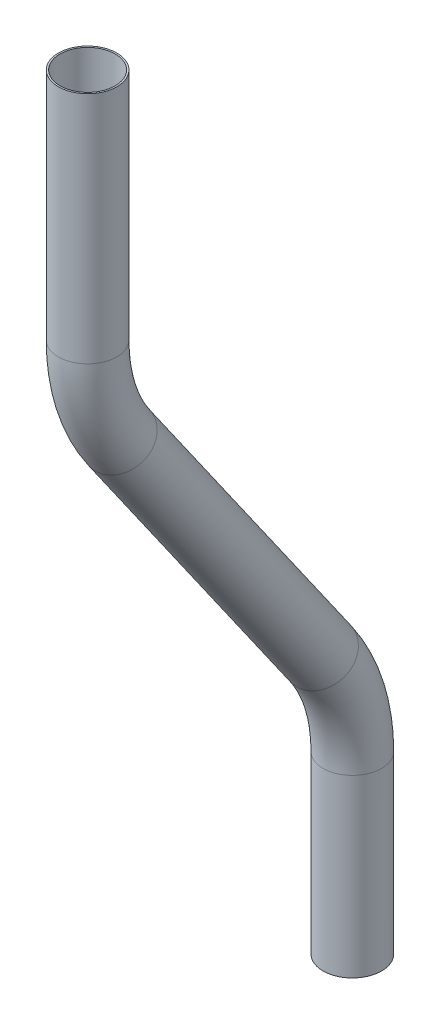
SolidWorks part; units mm, degrees
ref_plane "Front Plane" through (0, 0, 0) normal (0, 0, 1) x (1, 0, 0)
ref_plane "Top Plane" through (0, 0, 0) normal (0, 1, 0) x (1, 0, 0)
ref_plane "Right Plane" through (0, 0, 0) normal (1, 0, 0) x (0, 0, -1)
sketch "Sketch1" plane through (0, 0, 0) normal (0, 1, 0) x (1, 0, 0)
  circle A0 centre (0, 0) radius 6.35
  circle A1 centre (0, 0) radius 5.9958
  dimension "D1" = 12.7
  dimension "D2" = 11.9915
sketch "Sketch2" plane through (0, 0, 0) normal (1, 0, 0) x (0, 0, -1)
  line L0 (0, 0) -> (0, 38.1)
  line L1 (-6.8903, 59.9533) -> (-50.5968, 122.3726)
  line L2 (-57.4871, 144.2259) -> (-57.4871, 195.0259)
  arc A0 (0, 38.1) -> (-6.8903, 59.9533) centre (-38.1, 38.1) ccw
  arc A1 (-50.5968, 122.3726) -> (-57.4871, 144.2259) centre (-19.3871, 144.2259) cw
  dimension "D2" = 38.1
  dimension "D3" = 35
  dimension "D6" = 38.1
  dimension "D1" = 38.1
  dimension "D4" = 76.2
  dimension "D5" = 50.8
  dimension "D7" = 145
sweep "Sweep1" add profiles "Sketch1" path "Sketch2"
